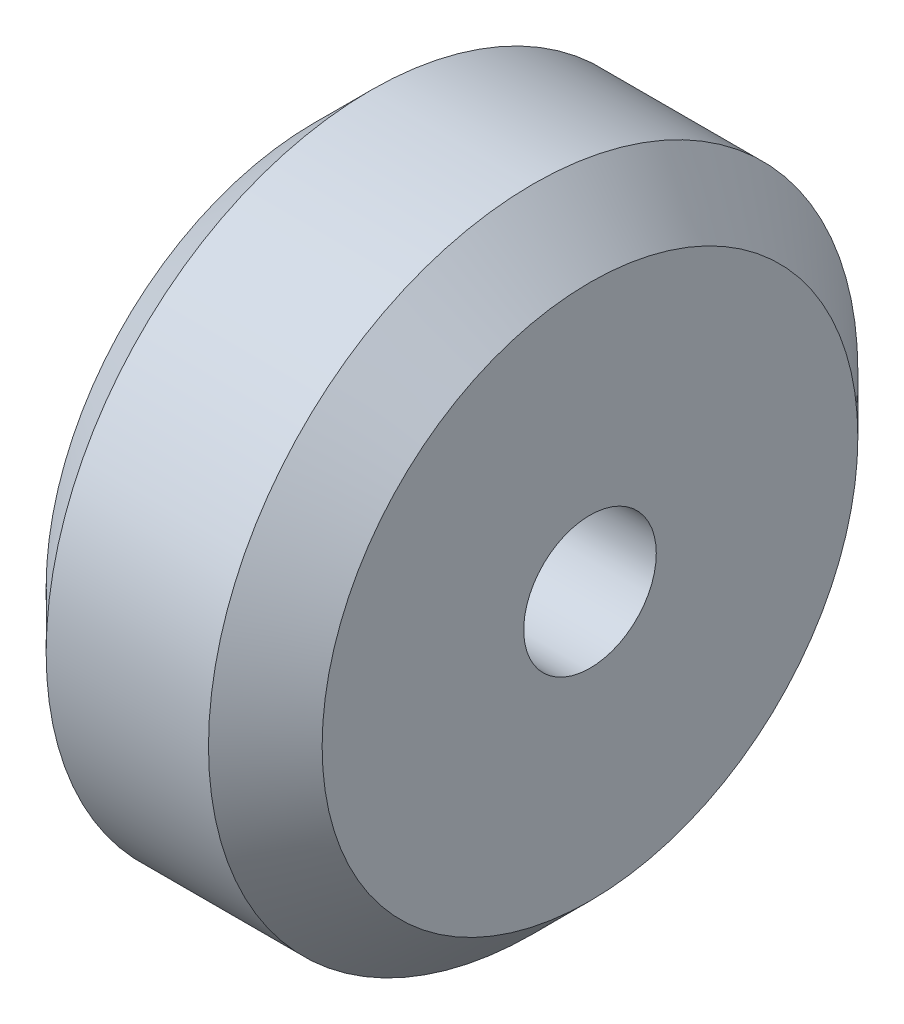
SolidWorks part; units mm, degrees
ref_plane "Alzado" through (0, 0, 0) normal (0, 0, 1) x (1, 0, 0)
ref_plane "Planta" through (0, 0, 0) normal (0, 1, 0) x (1, 0, 0)
ref_plane "Vista lateral" through (0, 0, 0) normal (1, 0, 0) x (0, 0, -1)
sketch "Croquis1" plane through (0, 0, 0) normal (0, 0, 1) x (1, 0, 0)
  line L95 (71.2935, 77.0421) -> (68.2935, 77.0421) construction
  line L96 (68.2935, 77.0421) -> (68.2935, 79.4921) construction
  line L97 (68.2935, 89.0421) -> (74.2935, 89.0421)
  line L98 (71.2935, 89.0421) -> (71.2935, 77.0421) construction
  line L99 (68.2935, 89.0421) -> (66.1935, 86.9421)
  line L100 (68.2935, 77.0421) -> (68.2935, 79.4921) construction
  line L101 (71.2935, 77.0421) -> (68.2935, 79.4921) construction
  line L102 (74.2935, 79.4921) -> (76.3935, 79.4921)
  line L103 (71.2935, 77.0421) -> (66.1935, 77.0421) construction
  line L104 (66.1935, 77.0421) -> (66.1935, 86.9421)
  line L105 (68.2935, 79.4921) -> (74.2935, 79.4921)
  line L106 (68.2935, 79.4921) -> (66.1935, 79.4921)
  line L107 (76.3935, 77.0421) -> (76.3935, 86.9421)
  line L108 (74.2935, 89.0421) -> (76.3935, 86.9421)
  line L109 (71.2935, 77.0421) -> (76.3935, 77.0421) construction
  point P15 (71.2935, 79.4921)
  dimension "D5" = 10.2
  dimension "D3" = 9.9
  dimension "D4" = 45
  dimension "D20" = 12
revolve "Revolución1" add sketch "Croquis1" angle 360 about L95
